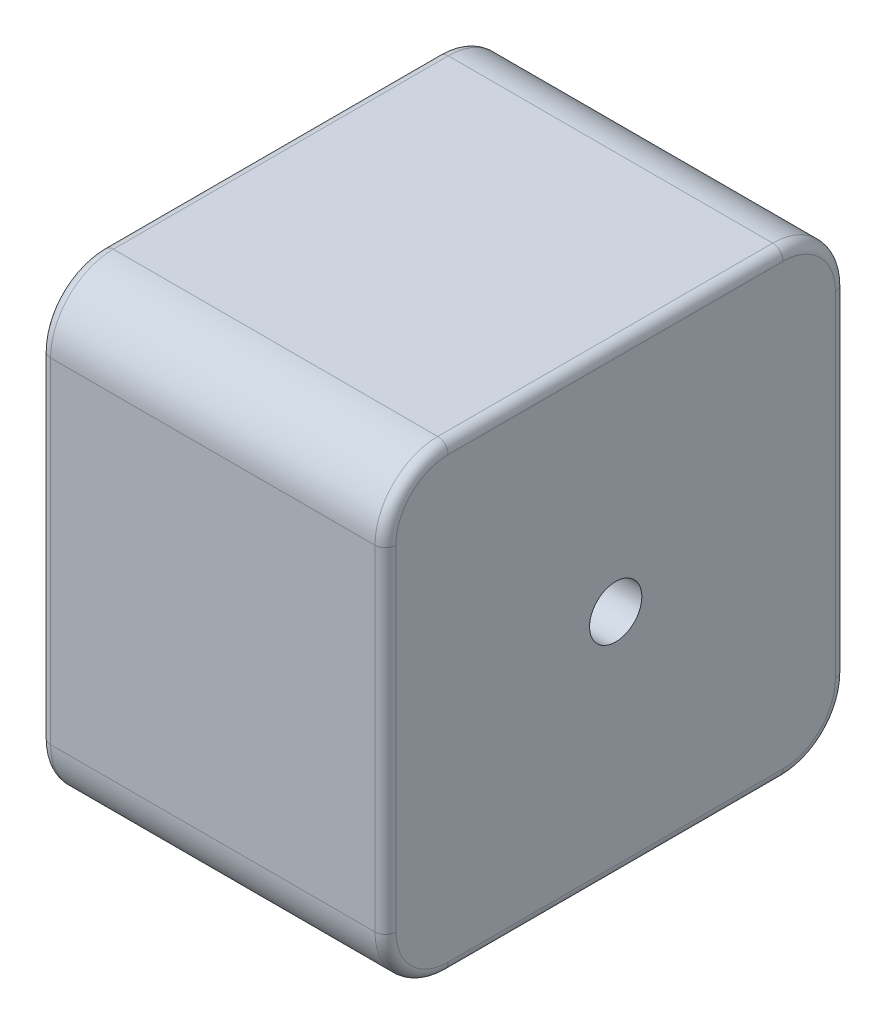
SolidWorks part; units mm, degrees
ref_plane "Front Plane" through (0, 0, 0) normal (0, 0, 1) x (1, 0, 0)
ref_plane "Top Plane" through (0, 0, 0) normal (0, 1, 0) x (1, 0, 0)
ref_plane "Right Plane" through (0, 0, 0) normal (1, 0, 0) x (0, 0, -1)
sketch "Sketch1" plane through (0, 0, 0) normal (1, 0, 0) x (0, 0, -1)
  line L1 (-16, 22) -> (16, 22)
  line L2 (-22, 16) -> (-22, -16)
  line L3 (-16, -22) -> (16, -22)
  line L4 (22, 16) -> (22, -16)
  circle A0 centre (0, 0) radius 2.5
  arc A1 (-22, -16) -> (-16, -22) centre (-16, -16) ccw
  arc A2 (16, -22) -> (22, -16) centre (16, -16) ccw
  arc A3 (16, 22) -> (22, 16) centre (16, 16) cw
  arc A4 (-16, 22) -> (-22, 16) centre (-16, 16) ccw
  point P4 (-22, 0)
  point P5 (0, 22)
  dimension "D1" = 6
extrude "Boss-Extrude1" add sketch "Sketch1" along normal blind 33
fillet "Fillet1" radius 1 16 edges at (0, 0, -22) (0, -20.2426, -20.2426) (0, -22, 0) (0, -20.2426, 20.2426) (0, 0, 22) (0, 20.2426, 20.2426) (33, 20.2426, 20.2426) (0, 22, 0) (0, 20.2426, -20.2426) (33, 0, 22) (33, -20.2426, 20.2426) (33, -22, 0) (33, -20.2426, -20.2426) (33, 0, -22) (33, 20.2426, -20.2426) (33, 22, 0)
